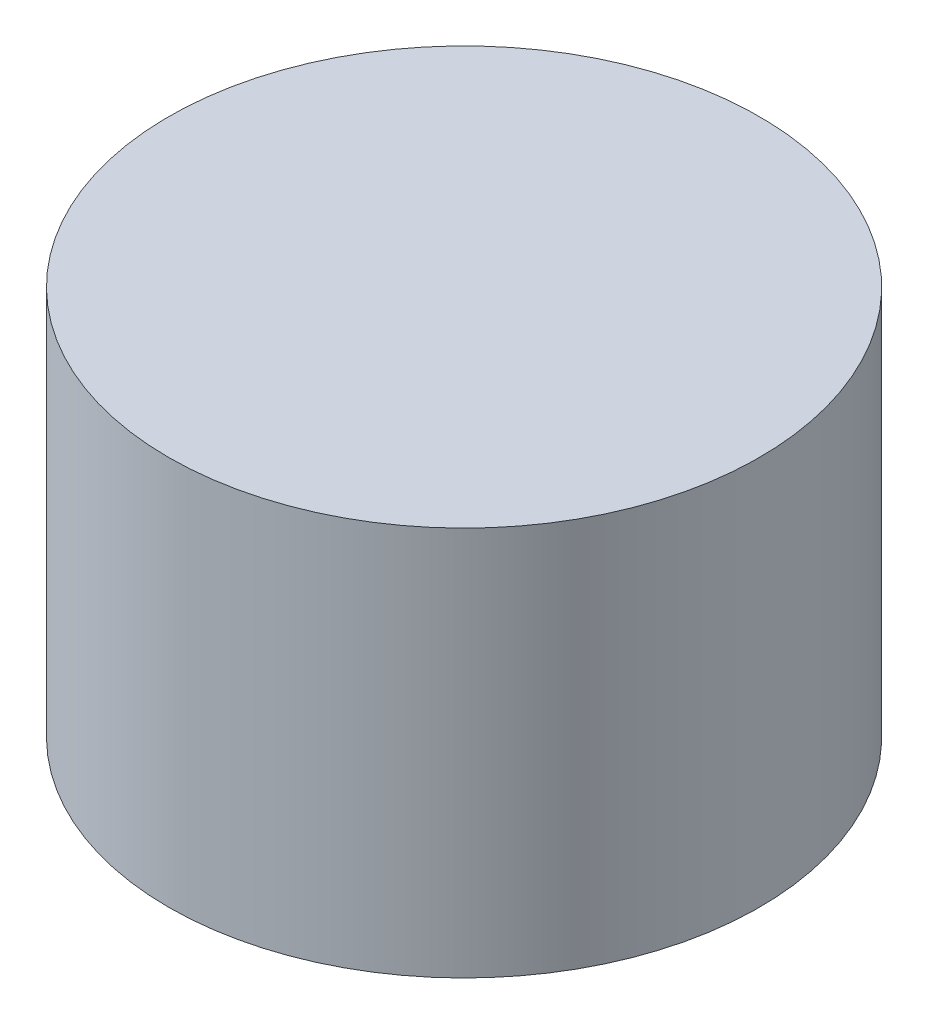
SolidWorks part; units mm, degrees
ref_plane "Front" through (0, 0, 0) normal (0, 0, 1) x (1, 0, 0)
ref_plane "Top" through (0, 0, 0) normal (0, 1, 0) x (1, 0, 0)
ref_plane "Right" through (0, 0, 0) normal (1, 0, 0) x (0, 0, -1)
sketch "Sketch1" plane through (0, 0, 0) normal (0, 1, 0) x (1, 0, 0)
  circle A0 centre (0, 0) radius 4.8129
  dimension "D1" = 9.6258
extrude "Boss-Extrude1" add sketch "Sketch1" along normal blind 6.35
